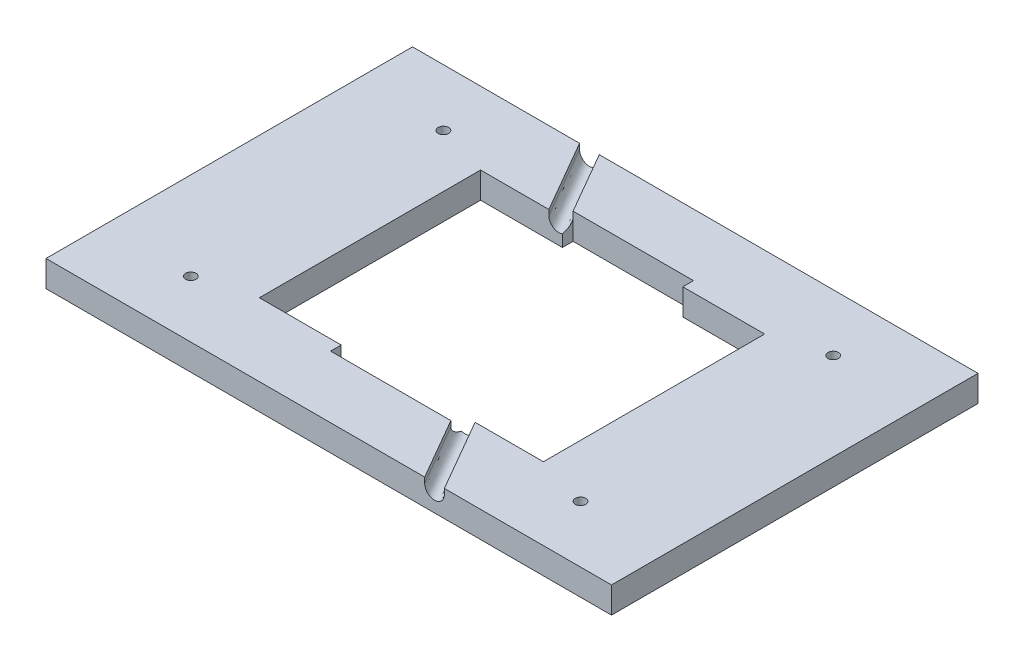
SolidWorks part; units mm, degrees
ref_plane "Piano frontale" through (0, 0, 0) normal (0, 0, 1) x (1, 0, 0)
ref_plane "Piano superiore" through (0, 0, 0) normal (0, 1, 0) x (1, 0, 0)
ref_plane "Piano destro" through (0, 0, 0) normal (1, 0, 0) x (0, 0, -1)
sketch "Schizzo1" plane through (0, 0, 0) normal (0, 1, 0) x (1, 0, 0)
  line L0 (16.9706, 21) -> (-16.9706, 21)
  line L1 (54, 35) -> (-54, 35)
  line L2 (54, 35) -> (54, -35)
  line L3 (54, -35) -> (-54, -35)
  line L4 (-54, 35) -> (-54, -35)
  line L5 (54, 35) -> (-54, -35) construction
  line L6 (54, -35) -> (-54, 35) construction
  line L7 (16.9706, -21) -> (-16.9706, -21)
  line L8 (-16.9706, -21) -> (-16.9706, 21)
  line L10 (16.9706, -21) -> (16.9706, 21)
  line L11 (-16.9706, -21) -> (16.9706, 21) construction
  line L12 (-16.9706, 21) -> (16.9706, -21) construction
  circle A0 centre (-37.2169, -24.1221) radius 8.125
  circle A1 centre (-37.2169, 24.1221) radius 8.125
  circle A2 centre (37.2169, 24.1221) radius 8.125
  circle A3 centre (37.2169, -24.1221) radius 8.125
  circle A4 centre (-37.2169, -24.1221) radius 1.5
  circle A5 centre (37.2169, -24.1221) radius 1.5
  circle A6 centre (37.2169, 24.1221) radius 1.5
  circle A7 centre (-37.2169, 24.1221) radius 1.5
  arc A8 (-16.9706, 21) -> (-16.9706, -21) centre (0, 0) ccw
  arc A9 (16.9706, 21) -> (16.9706, -21) centre (0, 0) cw
  point P0 (0, 0)
  dimension "D3" = 16.25
  dimension "D5" = 16.25
  dimension "D6" = 16.25
  dimension "D7" = 16.25
  dimension "D8" = 3
  dimension "D9" = 3
  dimension "D10" = 3
  dimension "D11" = 3
  dimension "D1" = 70
  dimension "D2" = 108
  dimension "D4" = 20
  dimension "D13" = 42
extrude "Estrusione-Estrusione2" add sketch "Schizzo1" along normal blind 5 contours L1 L4 L3 L2 A3 A2 A1 A0
sketch "Schizzo2" plane through (0, 5, 0) normal (0, 1, 0) x (1, 0, 0)
  line L0 (54, 35) -> (54, -35) construction
  line L2 (16.9706, 21) -> (-16.9706, 21) construction
  line L4 (16.9706, -21) -> (-16.9706, -21) construction
  line L5 (-10.25, 21) -> (14, -21) construction
  line L6 (14, -21) -> (22.0833, -35) construction
  line L7 (54, -35) -> (-54, -35) construction
  line L8 (22.0833, -35) -> (-18.3333, 35) construction
  line L9 (54, 35) -> (-54, 35) construction
  line L10 (-14.01, 21) -> (10.24, -21) construction
  line L11 (10.24, -21) -> (18.3233, -35) construction
  line L12 (18.3233, -35) -> (-22.0933, 35) construction
  line L13 (-22.0933, 35) -> (-18.3333, 35)
  line L14 (-18.3333, 35) -> (22.0833, -35)
  line L15 (22.0833, -35) -> (18.3233, -35)
  line L16 (18.3233, -35) -> (-22.0933, 35)
  point P0 (14, -21)
  point P3 (10.24, -21)
  point P5 (-10.25, 21)
  point P9 (-14.01, 21)
  dimension "D1" = 40
  dimension "D2" = 3.76
  dimension "D3" = 64.25
  dimension "D4" = 3.76
sketch "Schizzo5" plane through (0, 5, 0) normal (0, 1, 0) x (1, 0, 0)
  line L1 (-22.0933, 35) -> (18.3233, -35)
  line L3 (18.3233, -35) -> (22.0833, -35)
  line L4 (22.0833, -35) -> (-18.3333, 35)
  line L5 (-18.3333, 35) -> (-22.0933, 35)
extrude "Taglio-Estrusione4" cut sketch "Schizzo5" against normal blind 1
sketch "Schizzo7" plane through (0, 4, 0) normal (0, 1, 0) x (1, 0, 0)
  line L0 (-20.2133, 35) -> (20.2033, -35) construction
  line L1 (-18.3333, 35) -> (-22.0933, 35) construction
  line L2 (18.3233, -35) -> (22.0833, -35) construction
sketch "Schizzo8" plane through (0, 0, 35) normal (0, 0, 1) x (1, 0, 0)
  line L0 (18.3233, 4) -> (22.0833, 4) construction
  circle A0 centre (20.2033, 4) radius 1.88
extrude "Taglio-Estrusione5" cut sketch "Schizzo8" along direction (0.5, 0, 0.866) on the side against the normal blind 95
sketch "Schizzo9" plane through (0, 5, 0) normal (0, 1, 0) x (1, 0, 0)
  line L0 (-16.9706, 21) -> (36.3653, 21) construction
  line L1 (36.3653, 21) -> (-34.5885, 21) construction
  line L2 (-16.9706, -21) -> (34.4701, -21) construction
  line L3 (34.4701, -21) -> (-33.7594, -21) construction
  line L4 (-27, 0) -> (-27, 21) construction
  line L5 (27, 0) -> (27, -21) construction
  line L7 (-27, 21) -> (27, 21)
  line L8 (-27, 21) -> (-27, -21)
  line L9 (-27, -21) -> (27, -21)
  line L10 (27, 21) -> (27, -21)
  arc A0 (-16.9706, 21) -> (-16.9706, -21) centre (0, 0) ccw construction
  arc A1 (16.9706, -21) -> (16.9706, 21) centre (0, 0) ccw construction
extrude "Taglio-Estrusione6" cut sketch "Schizzo9" against normal blind 10
sketch "Schizzo10" plane through (0, 5, 0) normal (0, 1, 0) x (1, 0, 0)
  line L0 (-10.25, 21) -> (-18.3333, 35) construction
  line L1 (11.4944, -23.1552) -> (-11.4944, -23.1552)
  line L2 (11.4944, -23.1552) -> (11.4944, 23.1552)
  line L3 (11.4944, 23.1552) -> (-11.4944, 23.1552)
  line L4 (-11.4944, -23.1552) -> (-11.4944, 23.1552)
  line L5 (11.4944, -23.1552) -> (-11.4944, 23.1552) construction
  line L6 (11.4944, 23.1552) -> (-11.4944, -23.1552) construction
  point P0 (0, 0)
extrude "Taglio-Estrusione7" cut sketch "Schizzo10" against normal blind 10
sketch "Schizzo11" plane through (0, 5, 0) normal (0, 1, 0) x (1, 0, 0)
  line L1 (27.125, -21.125) -> (-27.125, -21.125)
  line L2 (27.125, -21.125) -> (27.125, 21.125)
  line L3 (27.125, 21.125) -> (-27.125, 21.125)
  line L4 (-27.125, -21.125) -> (-27.125, 21.125)
  line L5 (27.125, -21.125) -> (-27.125, 21.125) construction
  line L6 (27.125, 21.125) -> (-27.125, -21.125) construction
  point P0 (0, 0)
  dimension "D1" = 54.25
  dimension "D2" = 42.25
extrude "Taglio-Estrusione8" cut sketch "Schizzo11" against normal blind 10
sketch "Schizzo14" plane through (0, 5, 0) normal (0, 1, 0) x (1, 0, 0)
  line L0 (37.2169, 24.1221) -> (37.2169, -24.1221) construction
  circle A0 centre (37.2169, 24.1221) radius 8.125
  circle A1 centre (37.2169, -24.1221) radius 8.125
extrude "Estrusione-Estrusione3" add sketch "Schizzo14" against normal blind 2
sketch "Schizzo15" plane through (0, 5, 0) normal (0, 1, 0) x (1, 0, 0)
  line L0 (-37.2169, 24.1221) -> (-37.2169, -24.1221) construction
  circle A0 centre (-37.2169, 24.1221) radius 8.125
  circle A1 centre (-37.2169, -24.1221) radius 8.125
extrude "Estrusione-Estrusione4" add sketch "Schizzo15" against normal blind 2
sketch "Schizzo16" plane through (0, 0, 0) normal (0, -1, 0) x (1, 0, 0)
  line L0 (-37.2169, 15.9971) -> (-37.2169, -32.2471) construction
  line L1 (-37.2169, -32.2471) -> (37.2169, -32.2471) construction
  line L2 (37.2169, -32.2471) -> (37.2169, 32.2471) construction
  line L3 (37.2169, 32.2471) -> (-37.2169, 32.2471) construction
  line L4 (-37.2169, 32.2471) -> (-37.2169, 15.9971) construction
  line L5 (-46.2752, 16.4971) -> (48.2924, 16.4971) construction
  line L6 (-46.2752, 14.9971) -> (48.2924, 14.9971) construction
  line L7 (-78.0006, -15.1221) -> (65.6546, -15.1221) construction
  line L8 (-75.9857, -16.6221) -> (53.7473, -16.6221) construction
  line L9 (-40.0232, 16.4971) -> (-34.4107, 16.4971)
  line L10 (-34.4107, 16.4971) -> (-37.2169, 14.9971)
  line L11 (-37.2169, 14.9971) -> (-40.0232, 16.4971)
  line L12 (-40.0232, -16.6221) -> (-34.4107, -16.6221)
  line L13 (-34.4107, -16.6221) -> (-37.2169, -15.1221)
  line L14 (-37.2169, -15.1221) -> (-40.0232, -16.6221)
  line L15 (34.4107, 16.4971) -> (40.0232, 16.4971)
  line L16 (40.0232, 16.4971) -> (37.2169, 14.9971)
  line L17 (37.2169, 14.9971) -> (34.4107, 16.4971)
  line L18 (34.0919, -16.6221) -> (37.2169, -15.1221)
  line L19 (37.2169, -15.1221) -> (40.3419, -16.6221)
  line L20 (40.3419, -16.6221) -> (34.0919, -16.6221)
  circle A0 centre (-37.2169, 24.1221) radius 8.125 construction
  circle A1 centre (-37.2169, -24.1221) radius 8.125 construction
  circle A2 centre (37.2169, -24.1221) radius 8.125 construction
  circle A3 centre (37.2169, 24.1221) radius 8.125 construction
  circle A4 centre (-37.2169, -24.1221) radius 8.125 construction
  circle A5 centre (37.2169, 24.1221) radius 8.125 construction
  dimension "D1" = 0.5
  dimension "D2" = 1
  dimension "D3" = 9
  dimension "D4" = 1.5
extrude "Taglio-Estrusione10" cut sketch "Schizzo16" against normal blind 3
sketch "Schizzo17" plane through (0, 3, 0) normal (0, -1, 0) x (1, 0, 0)
  line L0 (-37.2169, 24.1221) -> (37.2169, 24.1221) construction
  line L1 (37.2169, 24.1221) -> (37.2169, -24.1221) construction
  line L2 (37.2169, -24.1221) -> (-37.2169, -24.1221) construction
  line L3 (-37.2169, -24.1221) -> (-37.2169, 24.1221) construction
  circle A0 centre (-37.2169, 24.1221) radius 1
  circle A1 centre (37.2169, 24.1221) radius 1
  circle A2 centre (37.2169, -24.1221) radius 1
  circle A3 centre (-37.2169, -24.1221) radius 1
  dimension "D1" = 2
  dimension "D2" = 2
  dimension "D3" = 2
  dimension "D4" = 2
extrude "Taglio-Estrusione11" cut sketch "Schizzo17" against normal blind 3
